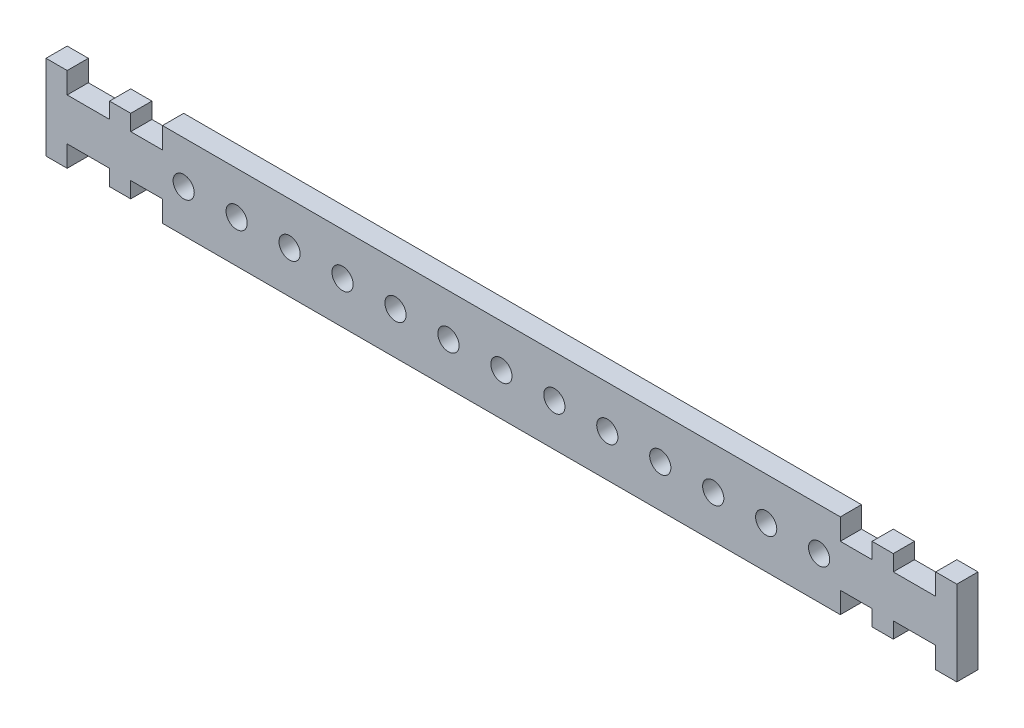
SolidWorks part; units mm, degrees
ref_plane "前视基准面" through (0, 0, 0) normal (0, 0, 1) x (1, 0, 0)
ref_plane "上视基准面" through (0, 0, 0) normal (0, 1, 0) x (1, 0, 0)
ref_plane "右视基准面" through (0, 0, 0) normal (1, 0, 0) x (0, 0, -1)
other "Configuration Table"
sketch "草图1" plane through (0, 0, 0) normal (0, 0, 1) x (1, 0, 0)
  line L0 (-42.9991, 0) -> (-39.6508, 0) construction
  line L1 (0.0009, 0) -> (0.0009, 8.5409) construction
  line L39 (-31.9991, 4) -> (32.0009, 4)
  line L40 (32.0009, 4) -> (32.0009, 2)
  line L41 (32.0009, 2) -> (35.0009, 2)
  line L42 (35.0009, 2) -> (35.0009, 3.5)
  line L43 (35.0009, 3.5) -> (37.0009, 3.5)
  line L44 (37.0009, 3.5) -> (37.0009, 2)
  line L45 (37.0009, 2) -> (41.0009, 2)
  line L46 (41.0009, 2) -> (41.0009, 4)
  line L47 (41.0009, 4) -> (43.0009, 4)
  line L48 (43.0009, 4) -> (43.0009, -4)
  line L49 (43.0009, -4) -> (41.0009, -4)
  line L50 (41.0009, -4) -> (41.0009, -2)
  line L51 (41.0009, -2) -> (37.0009, -2)
  line L52 (37.0009, -2) -> (37.0009, -3.5)
  line L53 (37.0009, -3.5) -> (35.0009, -3.5)
  line L54 (35.0009, -3.5) -> (35.0009, -2)
  line L55 (35.0009, -2) -> (32.0009, -2)
  line L56 (32.0009, -2) -> (32.0009, -4)
  line L57 (32.0009, -4) -> (-31.9991, -4)
  line L58 (-31.9991, -2) -> (-31.9991, -4)
  line L59 (-34.9991, -2) -> (-31.9991, -2)
  line L60 (-34.9991, -3.5) -> (-34.9991, -2)
  line L61 (-36.9991, -3.5) -> (-34.9991, -3.5)
  line L62 (-36.9991, -2) -> (-36.9991, -3.5)
  line L63 (-40.9991, -2) -> (-36.9991, -2)
  line L64 (-40.9991, -4) -> (-40.9991, -2)
  line L65 (-42.9991, -4) -> (-40.9991, -4)
  line L66 (-42.9991, 4) -> (-42.9991, -4)
  line L67 (-40.9991, 4) -> (-42.9991, 4)
  line L68 (-40.9991, 2) -> (-40.9991, 4)
  line L69 (-36.9991, 2) -> (-40.9991, 2)
  line L70 (-36.9991, 3.5) -> (-36.9991, 2)
  line L71 (-34.9991, 3.5) -> (-36.9991, 3.5)
  line L72 (-34.9991, 2) -> (-34.9991, 3.5)
  line L73 (-31.9991, 2) -> (-34.9991, 2)
  line L74 (-31.9991, 4) -> (-31.9991, 2)
  circle A9 centre (0.0009, 0) radius 1
  circle A18 centre (5.0009, 0) radius 1
  circle A19 centre (10.0009, 0) radius 1
  circle A20 centre (15.0009, 0) radius 1
  circle A21 centre (20.0009, 0) radius 1
  circle A22 centre (25.0009, 0) radius 1
  circle A23 centre (30.0009, 0) radius 1
  circle A24 centre (-4.9991, 0) radius 1
  circle A25 centre (-9.9991, 0) radius 1
  circle A26 centre (-14.9991, 0) radius 1
  circle A27 centre (-19.9991, 0) radius 1
  circle A28 centre (-24.9991, 0) radius 1
  circle A29 centre (-29.9991, 0) radius 1
  point P65 (0.0009, -4)
  point P101 (0.0009, 4)
  dimension "D27" = 2
  dimension "D17" = 32
  dimension "D18" = 2
  dimension "D19" = 3
  dimension "D20" = 1.5
  dimension "D21" = 4
  dimension "D22" = 2
  dimension "D23" = 2
  dimension "D24" = 2
  dimension "D25" = 8
  dimension "D26" = 64
  dimension "D30" = 74
  dimension "D28" = 7
  dimension "D29" = 7
extrude "凸台-拉伸1" add sketch "草图1" along normal blind 2
